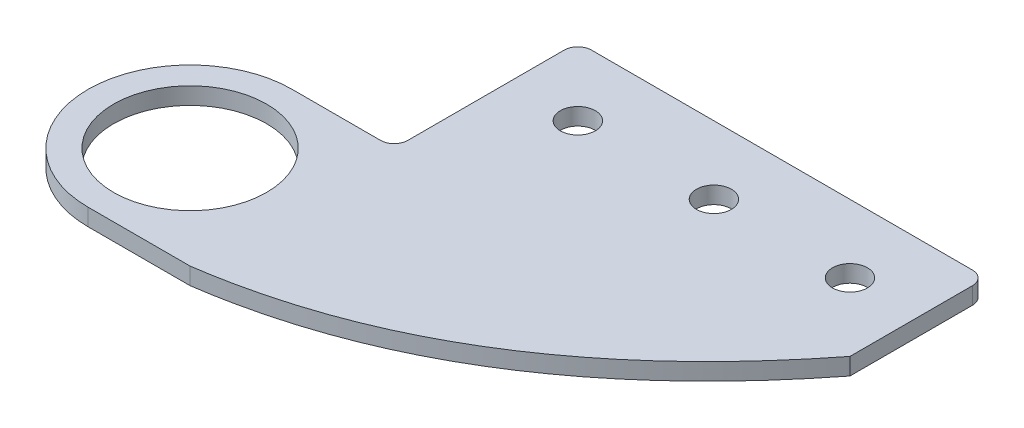
SolidWorks part; units mm, degrees
material "PC High Viscosity"
ref_plane "Front Plane" through (0, 0, 0) normal (0, 0, 1) x (1, 0, 0)
ref_plane "Top Plane" through (0, 0, 0) normal (0, 1, 0) x (1, 0, 0)
ref_plane "Right Plane" through (0, 0, 0) normal (1, 0, 0) x (0, 0, -1)
sketch "Sketch1" plane through (0, 0, 0) normal (0, 1, 0) x (1, 0, 0)
  line L0 (-57.15, -28.6938) -> (-38.1, -28.6938)
  line L6 (-57.15, -66.7938) -> (-38.1, -66.7938)
  line L7 (38.1, -19.8038) -> (6.35, -60.4438) construction
  line L10 (-38.1, 5.5962) -> (38.1, 5.5962)
  line L11 (38.1, -19.8038) -> (38.1, 5.5962)
  line L12 (6.35, -60.4438) -> (-38.1, -66.7938) construction
  line L16 (-38.1, 5.5962) -> (-38.1, -45.2038)
  circle A5 centre (-57.15, -47.7438) radius 14.2875
  circle A9 centre (25.4, -7.1038) radius 3.2639
  circle A10 centre (0, -7.1038) radius 3.2639
  circle A11 centre (-25.4, -7.1038) radius 3.2639
  arc A12 (-57.15, -66.7938) -> (-57.15, -28.6938) centre (-57.15, -47.7438) cw
  spline S0 degree 2 poles (38.1, -19.8038) (6.35, -60.4438) (-38.1, -66.7938) knots 0 0 0 1 1 1
  point P16 (6.35, -73.1438)
  point P32 (-38.1, -35.0438)
  dimension "D2" = 12.7
  dimension "D4" = 12.7
  dimension "D8" = 28.575
  dimension "D12" = 40.64
  dimension "D3" = 6.5278
  dimension "D10" = 19.05
  dimension "D5" = 3
  dimension "D6" = 95.25
  dimension "D7" = 50.8
  dimension "D9" = 31.75
  dimension "D14" = 76.2
  dimension "D15" = 25.4
  dimension "D18" = 0
  dimension "D11" = 19.05
extrude "Boss-Extrude1" add sketch "Sketch1" along normal blind 3.175
fillet "Fillet1" radius 2.54 3 edges at (38.1, 1.5875, -5.5962) (-38.1, 1.5875, -5.5962) (-38.1, 1.5875, 28.6938)
